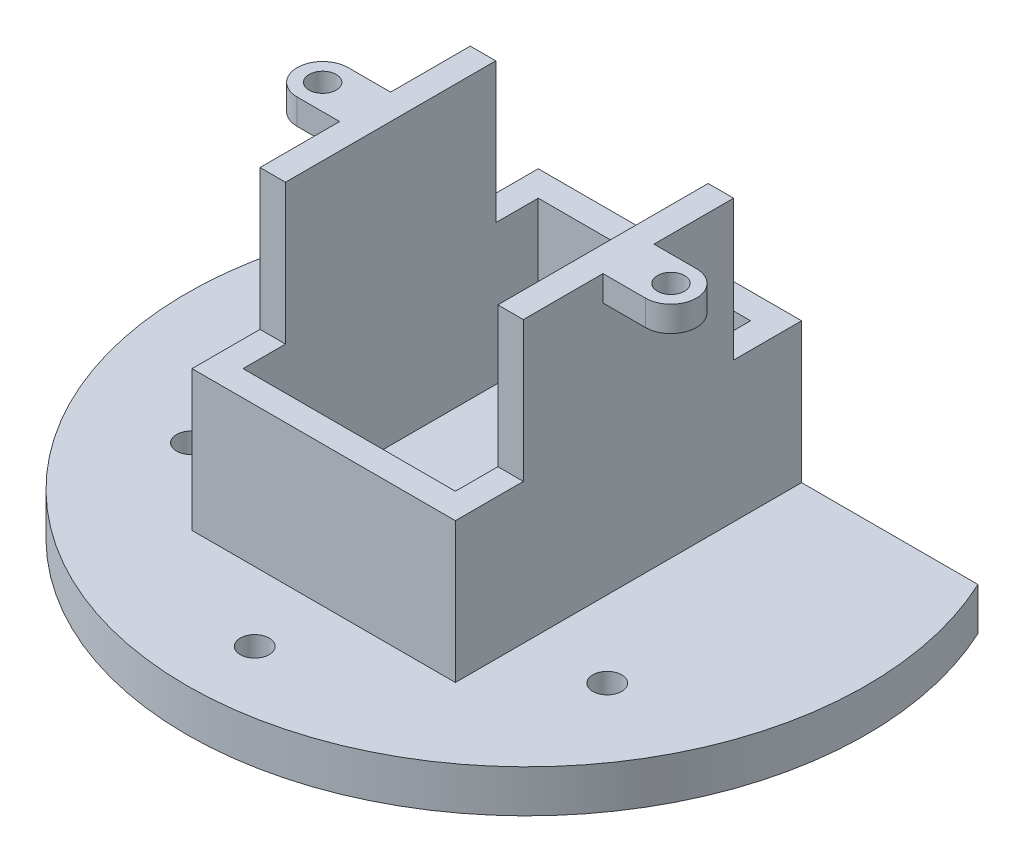
SolidWorks part; units mm, degrees
ref_plane "前视基准面" through (0, 0, 0) normal (0, 0, 1) x (1, 0, 0)
ref_plane "上视基准面" through (0, 0, 0) normal (0, 1, 0) x (1, 0, 0)
ref_plane "右视基准面" through (0, 0, 0) normal (1, 0, 0) x (0, 0, -1)
sketch "草图1" plane through (0, 0, 0) normal (0, 0, 1) x (1, 0, 0)
  line L1 (0, 0) -> (31, 0)
  line L2 (0, 0) -> (0, 38)
  line L3 (0, 38) -> (31, 38)
  line L4 (31, 0) -> (31, 38)
  dimension "D1" = 38
  dimension "D2" = 31
extrude "凸台-拉伸1" add sketch "草图1" against normal blind 40.75
sketch "草图2" plane through (31, 0, 0) normal (1, 0, 0) x (0, 0, -1)
  line L1 (40.75, 38) -> (32.75, 38)
  line L2 (40.75, 38) -> (40.75, 21.5)
  line L3 (40.75, 21.5) -> (32.75, 21.5)
  line L4 (32.75, 38) -> (32.75, 21.5)
  dimension "D1" = 16.5
  dimension "D2" = 8
extrude "切除-拉伸1" cut sketch "草图2" against normal blind 40.75
sketch "草图3" plane through (0, 38, 0) normal (0, 1, 0) x (1, 0, 0)
  line L0 (0, 40.75) -> (31, 0) construction
  line L1 (31, 40.75) -> (0, 40.75) construction
  line L2 (3, 3) -> (28, 3)
  line L3 (3, 3) -> (3, 37.75)
  line L4 (3, 37.75) -> (28, 37.75)
  line L5 (28, 3) -> (28, 37.75)
  line L6 (15.5, 37.75) -> (15.5, 3) construction
  line L7 (3, 20.375) -> (28, 20.375) construction
  line L8 (31, 32.75) -> (31, 0) construction
  point P4 (15.5, 20.375)
  dimension "D1" = 3
  dimension "D2" = 3
extrude "切除-拉伸2" cut sketch "草图3" against normal blind 34.5
sketch "草图4" plane through (0, 0, 0) normal (0, 0, 1) x (1, 0, 0)
  line L0 (31, 38) -> (0, 38) construction
  circle A0 centre (15.5, 38) radius 12.5
  dimension "D1" = 25
extrude "切除-拉伸3" cut sketch "草图4" against normal blind 34.5
sketch "草图5" plane through (0, 38, 0) normal (0, 1, 0) x (1, 0, 0)
  line L0 (0, 40.75) -> (31, 0) construction
  line L1 (15.5, 20.375) -> (15.5, 40.75) construction
  line L2 (15.5, 20.375) -> (31, 20.375) construction
  line L3 (31, 32.75) -> (31, 0) construction
  line L4 (36, 23.375) -> (31, 23.375)
  line L5 (31, 23.375) -> (31, 17.375)
  line L6 (31, 17.375) -> (36, 17.375)
  line L7 (0, 23.375) -> (0, 17.375)
  line L8 (0, 17.375) -> (-5, 17.375)
  line L9 (-5, 23.375) -> (0, 23.375)
  circle A0 centre (36, 20.375) radius 1.6
  arc A1 (36, 17.375) -> (36, 23.375) centre (36, 20.375) ccw
  arc A2 (-5, 17.375) -> (-5, 23.375) centre (-5, 20.375) cw
  circle A3 centre (-5, 20.375) radius 1.6
  dimension "D1" = 3.2
  dimension "D2" = 6
  dimension "D3" = 5
extrude "凸台-拉伸2" add sketch "草图5" against normal blind 3
sketch "草图8" plane through (0, 0, 0) normal (0, -1, 0) x (1, 0, 0)
  line L0 (15.5, 0) -> (15.5, -49.4641) construction
  line L1 (0, 0) -> (31, 0) construction
  line L2 (-20.7662, -40.75) -> (51.7662, -40.75)
  line L3 (0, -40.75) -> (31, -40.75) construction
  arc A0 (51.7662, -40.75) -> (-20.7662, -40.75) centre (15.5, -23.875) ccw
  dimension "D2" = 40
  dimension "D1" = 23.875
extrude "凸台-拉伸5" add sketch "草图8" against normal blind 5
sketch "草图9" plane through (0, 5, 0) normal (0, 1, 0) x (1, 0, 0)
  line L0 (-24.5, 23.875) -> (55.5, 23.875) construction
  line L1 (15.5, 40.75) -> (15.5, -16.125) construction
  line L2 (31, 40.75) -> (0, 40.75) construction
  circle A1 centre (40, 8.875) radius 1.7
  arc A4 (-20.7662, 40.75) -> (51.7662, 40.75) centre (15.5, 23.875) ccw construction
  circle A5 centre (-9, 8.875) radius 1.7
  point P18 (40, 38.875)
  point P19 (40, 8.875)
  dimension "D1" = 49
  dimension "D2" = 30
  dimension "D3" = 3.4
extrude "切除-拉伸4" cut sketch "草图9" against normal blind 10
sketch "草图11" plane through (0, 5, 0) normal (0, 1, 0) x (1, 0, 0)
  line L0 (15.5, 23.875) -> (15.5, -20.0791) construction
  circle A0 centre (15.5, -8.125) radius 1.7
  point P5 (0, 0)
  dimension "D1" = 32
  dimension "D2" = 3.4
extrude "切除-拉伸5" cut sketch "草图11" against normal blind 10
sketch "草图12" plane through (0, 0, 0) normal (0, 0, 1) x (1, 0, 0)
  line L1 (0, 38) -> (31, 38)
  line L2 (0, 38) -> (0, 21.5)
  line L3 (0, 21.5) -> (31, 21.5)
  line L4 (31, 38) -> (31, 21.5)
  dimension "D1" = 16.5
extrude "切除-拉伸6" cut sketch "草图12" against normal blind 8
